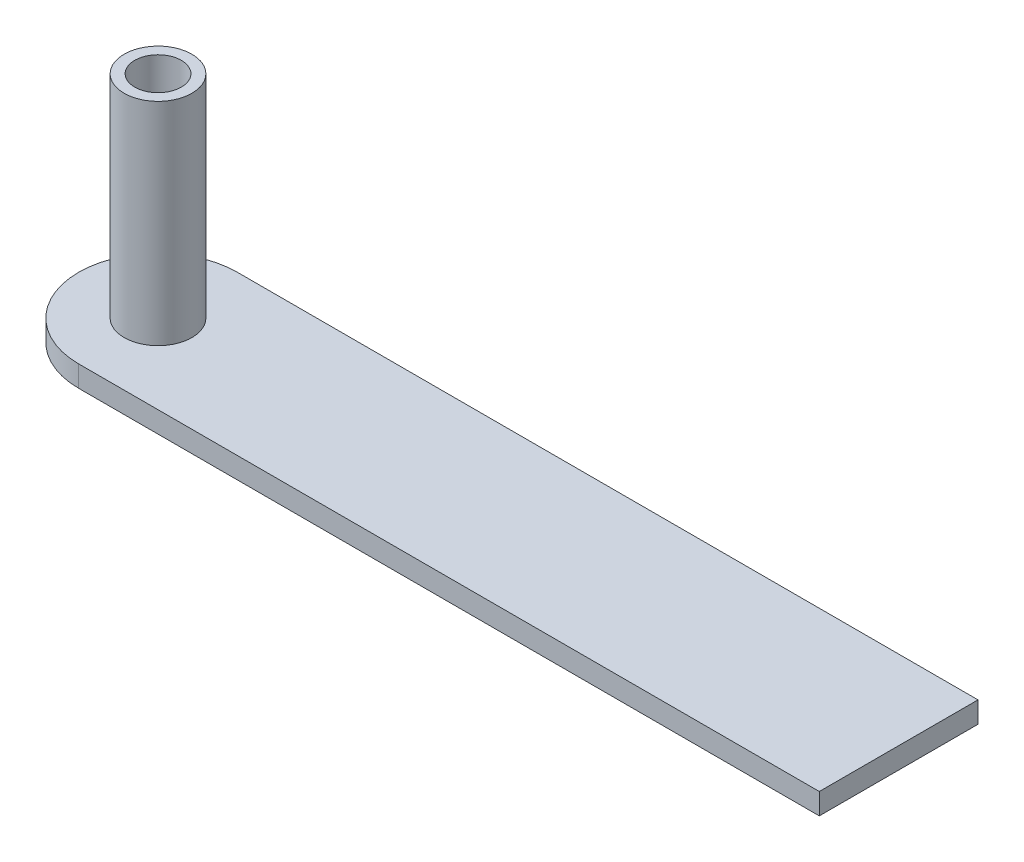
SolidWorks part; units mm, degrees
other "Markup1"
sketch "Sketch7" plane through (85, 46, 0) normal (0.169, 0.6393, 0.7502) x (0.9761, -0.0032, -0.2172)
ref_plane "Front Plane" through (0, 0, 0) normal (0, 0, 1) x (1, 0, 0)
ref_plane "Top Plane" through (0, 0, 0) normal (0, 1, 0) x (1, 0, 0)
ref_plane "Right Plane" through (0, 0, 0) normal (1, 0, 0) x (0, 0, -1)
sketch "Sketch1" plane through (0, 0, 0) normal (0, 1, 0) x (1, 0, 0)
  line L1 (0, 0) -> (70, 0)
  line L2 (0, 0) -> (0, 15)
  line L3 (0, 15) -> (70, 15)
  line L4 (70, 0) -> (70, 15)
  dimension "D1" = 15
  dimension "D2" = 70
extrude "Boss-Extrude1" add sketch "Sketch1" along normal blind 2
sketch "Sketch2" plane through (0, 2, 0) normal (0, 1, 0) x (1, 0, 0)
  line L0 (0, 0) -> (0, 15) construction
  circle A0 centre (0, 7.5) radius 7.5
extrude "Boss-Extrude2" add sketch "Sketch2" along normal blind 2 from offset 2 offset against normal yes
sketch "Sketch3" plane through (0, 2, 0) normal (0, 1, 0) x (1, 0, 0)
  circle A0 centre (0, 7.5) radius 3.2
  circle A1 centre (0, 7.5) radius 2.4
extrude "Boss-Extrude5" add sketch "Sketch3" along normal blind 20
sketch "Sketch10" plane through (0, 2, 0) normal (0, 1, 0) x (1, 0, 0)
  circle A0 centre (0, 7.5) radius 2.4
extrude "Cut-Extrude1" cut sketch "Sketch10" against normal blind 16
sketch "Sketch11" plane through (0, 22, 0) normal (0, 1, 0) x (1, 0, 0)
  circle A0 centre (0, 7.5) radius 2.1998
  circle A1 centre (0, 7.5) radius 3.2
extrude "Boss-Extrude6" add sketch "Sketch11" against normal blind 22
sketch "Sketch12" plane through (0, 22, 0) normal (0, 1, 0) x (1, 0, 0)
  circle A0 centre (0, 7.5) radius 2.2
  circle A1 centre (0, 7.5) radius 2
extrude "Boss-Extrude8" add sketch "Sketch12" against normal blind 22
sketch "Sketch13" plane through (0, 22, 0) normal (0, 1, 0) x (1, 0, 0)
  circle A0 centre (0, 7.5) radius 2.3
  circle A1 centre (0, 7.5) radius 2.2
extrude "Cut-Extrude2" cut sketch "Sketch13" against normal blind 4 contours A1
sketch "Sketch14" plane through (0, 0, 0) normal (0, -1, 0) x (1, 0, 0)
  circle A0 centre (0, -7.5) radius 2
  circle A1 centre (0, -7.5) radius 2.5
extrude "Cut-Extrude4" cut sketch "Sketch14" against normal blind 17
